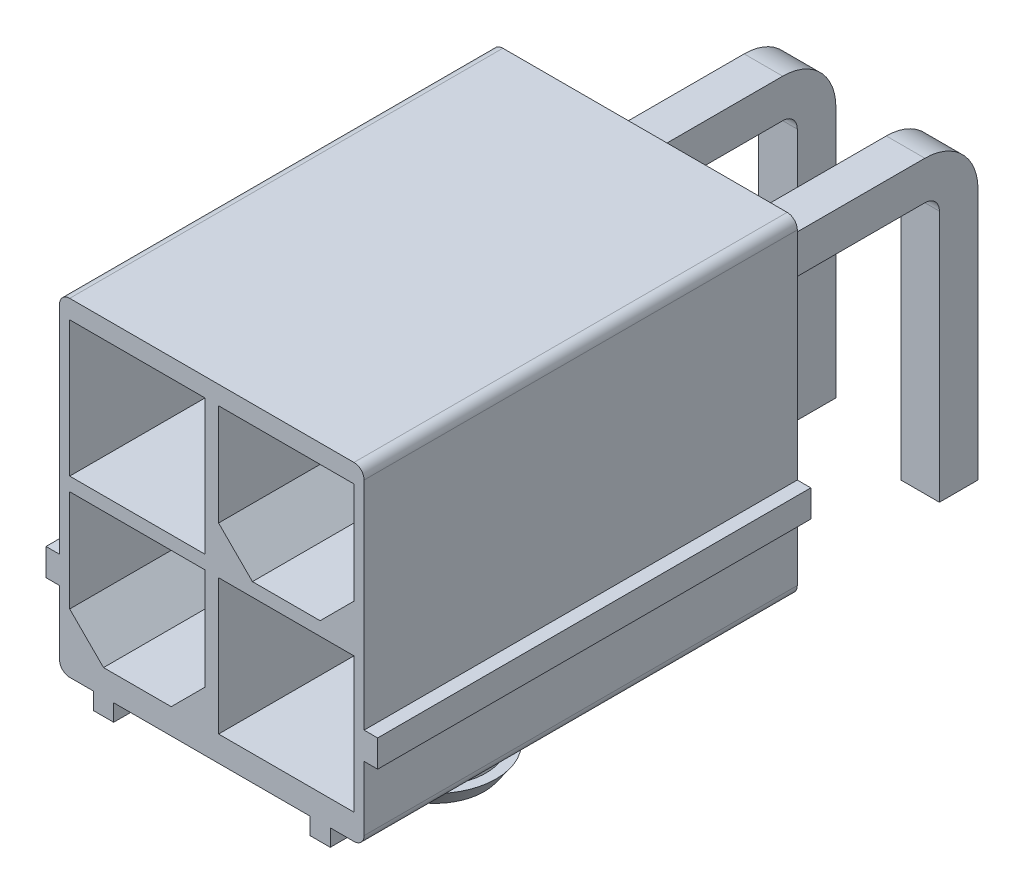
SolidWorks part; units mm, degrees
ref_plane "Front Plane" through (0, 0, 0) normal (0, 0, 1) x (1, 0, 0)
ref_plane "Top Plane" through (0, 0, 0) normal (0, 1, 0) x (1, 0, 0)
ref_plane "Right Plane" through (0, 0, 0) normal (1, 0, 0) x (0, 0, -1)
sketch "Sketch1" plane through (0, 0, 0) normal (0, 0, 1) x (1, 0, 0)
  line L0 (0, 0) -> (0, 0.5) construction
  line L1 (-4.5, 0.5) -> (-3.5, 0.5)
  line L2 (-4.5, 0.5) -> (-4.5, 2.7)
  line L3 (-4.5, 10.2) -> (4.5, 10.2)
  line L4 (4.5, 0.5) -> (4.5, 2.7)
  line L5 (4.5, 2.7) -> (4.9, 2.7)
  line L6 (4.9, 2.7) -> (4.9, 3.5)
  line L7 (4.9, 3.5) -> (4.5, 3.5)
  line L8 (-4.5, 2.7) -> (-4.9, 2.7)
  line L9 (-4.9, 2.7) -> (-4.9, 3.5)
  line L10 (-4.9, 3.5) -> (-4.5, 3.5)
  line L11 (2.9, 0) -> (0, 0) construction
  line L12 (3.5, 0.5) -> (4.5, 0.5)
  line L13 (2.9, 0.5) -> (2.9, 0)
  line L14 (2.9, 0) -> (3.5, 0)
  line L15 (3.5, 0.5) -> (3.5, 0)
  line L17 (-3.5, 0.5) -> (-3.5, 0)
  line L18 (-3.5, 0) -> (-2.9, 0)
  line L19 (-2.9, 0.5) -> (-2.9, 0)
  line L20 (0, 0) -> (-2.9, 0) construction
  line L22 (4.5, 3.5) -> (4.5, 10.2)
  line L23 (-4.5, 3.5) -> (-4.5, 10.2)
  line L24 (-2.9, 0.5) -> (2.9, 0.5)
  dimension "D1" = 9.7
  dimension "D2" = 9
  dimension "D3" = 0.5
  dimension "D4" = 0.4
  dimension "D5" = 0.8
  dimension "D6" = 3
  dimension "D7" = 0.6
  dimension "D8" = 1
  dimension "D9" = 1
extrude "Boss-Extrude1" add sketch "Sketch1" against normal blind 12.8
ref_plane "Plane1" through (2.1, 0, 0) normal (1, 0, 0) x (0, 0, -1)
ref_plane "Plane2" through (-2.1, 0, 0) normal (1, 0, 0) x (0, 0, -1)
sketch "Sketch2" plane through (0, 0, -12.8) normal (0, 0, -1) x (-1, 0, 0)
  line L0 (1.53, 6.88) -> (2.67, 8.02) construction
  line L1 (-2.67, 8.02) -> (-1.53, 8.02)
  line L2 (-2.67, 8.02) -> (-2.67, 6.88)
  line L3 (-2.67, 6.88) -> (-1.53, 6.88)
  line L4 (-1.53, 8.02) -> (-1.53, 6.88)
  line L5 (1.53, 8.02) -> (2.67, 8.02) construction
  line L6 (1.53, 8.02) -> (1.53, 6.88) construction
  line L7 (1.53, 6.88) -> (2.67, 6.88) construction
  line L8 (2.67, 8.02) -> (2.67, 6.88) construction
  line L9 (-2.67, 3.82) -> (-1.53, 3.82) construction
  line L10 (-2.67, 3.82) -> (-2.67, 2.68) construction
  line L11 (-2.67, 2.68) -> (-1.53, 2.68) construction
  line L12 (-1.53, 3.82) -> (-1.53, 2.68) construction
  line L13 (1.53, 3.82) -> (2.67, 3.82) construction
  line L14 (1.53, 3.82) -> (1.53, 2.68) construction
  line L15 (1.53, 2.68) -> (2.67, 2.68) construction
  line L16 (2.67, 3.82) -> (2.67, 2.68) construction
  line L17 (-2.67, 6.88) -> (-1.53, 8.02) construction
  line L18 (-2.67, 2.68) -> (-1.53, 3.82) construction
  line L19 (1.53, 2.68) -> (2.67, 3.82) construction
  line L20 (-2.1, 6.16) -> (-2.1, -6.16) construction
  line L21 (2.1, 6.16) -> (2.1, -6.16) construction
  line L22 (-2.1, 7.45) -> (2.1, 7.45) construction
  line L23 (-2.1, 3.25) -> (2.1, 3.25) construction
  line L24 (-4.5, 0.5) -> (4.5, 10.2) construction
  line L25 (2.1, 3.25) -> (-2.1, 7.45) construction
  point P16 (-2.1, 7.45)
  point P17 (2.1, 7.45)
  point P18 (2.1, 3.25)
  point P19 (-2.1, 3.25)
  point P32 (0, 5.35)
  dimension "D1" = 4.2
  dimension "D2" = 1.14
sketch "Sketch3" plane through (2.1, 0, 0) normal (1, 0, 0) x (0, 0, -1)
  line L0 (12.8, 7.45) -> (18.4, 7.45)
  line L1 (19.4, 6.45) -> (19.4, -1)
  line L2 (12.8, 0) -> (0, 0) construction
  line L3 (12.8, 0.5) -> (12.8, 10.2) construction
  arc A0 (19.4, 6.45) -> (18.4, 7.45) centre (18.4, 6.45) ccw
  dimension "D3" = 1
  dimension "D1" = 1
  dimension "D2" = 6.6
sketch "Sketch4" plane through (0, 0, -12.8) normal (0, 0, -1) x (-1, 0, 0)
  line L1 (-2.67, 3.82) -> (-1.53, 3.82)
  line L2 (-2.67, 3.82) -> (-2.67, 2.68)
  line L3 (-2.67, 2.68) -> (-1.53, 2.68)
  line L4 (-1.53, 3.82) -> (-1.53, 2.68)
sketch "Sketch5" plane through (2.1, 0, 0) normal (1, 0, 0) x (0, 0, -1)
  line L0 (12.8, 3.25) -> (12.9, 3.25)
  line L1 (13.9, 2.25) -> (13.9, -1)
  line L3 (12.8, 3.5) -> (12.8, 10.2) construction
  arc A0 (12.9, 3.25) -> (13.9, 2.25) centre (12.9, 2.25) cw
  dimension "D2" = 1
  dimension "D1" = 1.1
sweep "Sweep2" add profiles "Sketch2" path "Sketch3"
sweep "Sweep3" add profiles "Sketch4" path "Sketch5"
pattern_linear "LPattern2" count 2 spacing 4.2 along (-1, 0, 0) of "Sweep2"
pattern_linear "LPattern3" count 2 spacing 4.2 along (-1, 0, 0) of "Sweep3"
fillet "Fillet1" radius 0.3 4 edges at (-4.5, 0.5, -6.4) (4.5, 0.5, -6.4) (-4.5, 10.2, -6.4) (4.5, 10.2, -6.4)
sketch "Sketch6" plane through (0, 0, 0) normal (0, 0, 1) x (1, 0, 0)
  line L0 (-4.2, 2.25) -> (-3.2, 1.25)
  line L1 (-4.2, 9.65) -> (-0.2, 9.65)
  line L2 (-4.2, 9.65) -> (-4.2, 5.65)
  line L3 (-4.2, 5.65) -> (-0.2, 5.65)
  line L4 (-0.2, 9.65) -> (-0.2, 5.65)
  line L5 (0.2, 5.25) -> (4.2, 5.25)
  line L6 (0.2, 5.25) -> (0.2, 1.25)
  line L7 (0.2, 1.25) -> (4.2, 1.25)
  line L8 (4.2, 5.25) -> (4.2, 1.25)
  line L9 (0.2, 9.65) -> (4.2, 9.65)
  line L10 (0.2, 9.65) -> (0.2, 6.65)
  line L11 (1.2, 5.65) -> (3.2, 5.65)
  line L12 (4.2, 9.65) -> (4.2, 6.65)
  line L13 (-4.2, 5.25) -> (-0.2, 5.25)
  line L14 (-4.2, 5.25) -> (-4.2, 2.25)
  line L15 (-3.2, 1.25) -> (-1.2, 1.25)
  line L16 (-0.2, 5.25) -> (-0.2, 2.25)
  line L17 (-1.2, 1.25) -> (-0.2, 2.25)
  line L18 (0.2, 6.65) -> (1.2, 5.65)
  line L19 (4.2, 6.65) -> (3.2, 5.65)
  line L20 (2.2, 5.65) -> (2.2, 7.271) construction
  line L21 (-2.2, 1.25) -> (-2.2, 2.2904) construction
  line L22 (0, 0.5) -> (0, 10.2) construction
  line L26 (-2.9, 0.5) -> (2.9, 0.5) construction
  line L27 (4.2, 10.2) -> (-4.2, 10.2) construction
  line L28 (0, 5.35) -> (0.8923, 5.35) construction
  dimension "D1" = 4
  dimension "D2" = 4
  dimension "D3" = 1
  dimension "D4" = 1
  dimension "D5" = 0.4
  dimension "D6" = 0.3
  dimension "D7" = 0.4
extrude "Cut-Extrude1" cut sketch "Sketch6" against normal blind 12
sketch "Sketch8" plane through (0, 0, 0) normal (1, 0, 0) x (0, 0, -1)
  line L0 (5.6, 0.5) -> (5.6, -2.9)
  line L1 (12.8, 0.5) -> (0, 0.5) construction
  line L2 (5.6, -2.9) -> (5.1501, -2.9)
  line L3 (5.1501, -2.9) -> (4.8, -2.4)
  line L4 (4.8, -2.4) -> (5.1, -2.4)
  line L5 (5.1, -2.4) -> (5.1, 0.5)
  line L6 (12.8, 0.5) -> (0, 0.5) construction
  line L7 (5.1, 0.5) -> (5.6, 0.5)
  line L8 (6.6, 0.5) -> (6.6, -3.7269) construction
  line L9 (14.47, -1) -> (13.33, -1) construction
  line L12 (12.8, 0) -> (0, 0) construction
  point P12 (13.9, -1)
  dimension "D1" = 7.3
  dimension "D2" = 1.5
  dimension "D3" = 0.5
  dimension "D4" = 2.9
  dimension "D5" = 55
  dimension "D6" = 0.8
  dimension "D7" = 0.5
revolve "Revolve1" add sketch "Sketch8" angle 360 about L8
sketch "Sketch9" plane through (0, 0, 0) normal (0, 0, 1) x (1, 0, 0)
  line L0 (-1.5, 0.5) -> (1.5, 0.5) construction
  line L1 (-0.8, 0.5) -> (0.8, 0.5)
  line L2 (-0.8, 0.5) -> (-0.8, -3)
  line L3 (-0.8, -3) -> (0.8, -3)
  line L4 (0.8, 0.5) -> (0.8, -3)
  line L5 (0, 0) -> (0, 0.5) construction
  dimension "D1" = 1.6
  dimension "D2" = 3.5
extrude "Cut-Extrude2" cut sketch "Sketch9" against normal through all
